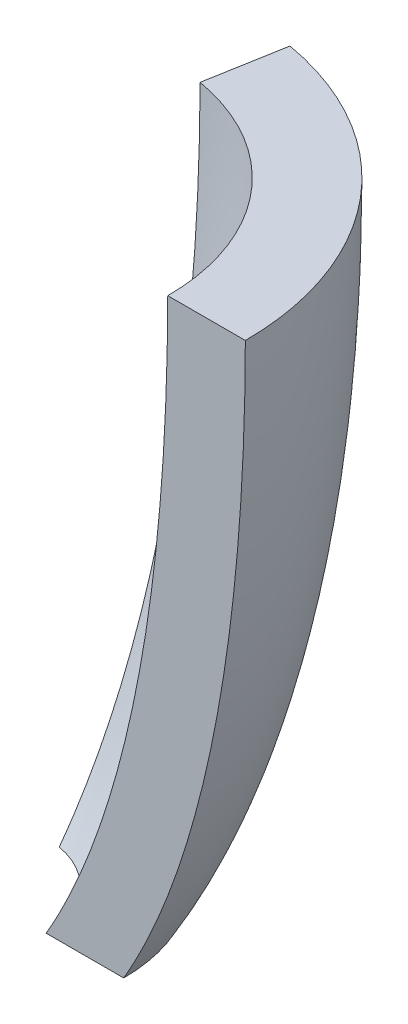
SolidWorks part; units mm, degrees
ref_plane "Front Plane" through (0, 0, 0) normal (0, 0, 1) x (1, 0, 0)
ref_plane "Top Plane" through (0, 0, 0) normal (0, 1, 0) x (1, 0, 0)
ref_plane "Right Plane" through (0, 0, 0) normal (1, 0, 0) x (0, 0, -1)
sketch "Sketch1" plane through (0, 0, 0) normal (0, 0, 1) x (1, 0, 0)
  line L0 (0, 0) -> (35, 0) construction
  line L1 (0, 0) -> (0, -93.4) construction
  line L2 (36.3, 0) -> (26.3, 0)
  line L4 (35, 0) -> (36.3, 0) construction
  line L5 (0, -93.4) -> (0, -94.7)
  line L6 (20.6222, -79.0125) -> (10.6222, -79.0125)
  spline S0 degree 3 poles (26.3, 0) (26.2301, -33.296) (21.1355, -60.9232) (10.6222, -79.0125) knots 0 0 0 0 1 1 1 1
  spline S2 degree 3 poles (36.3, 0) (36.2301, -33.296) (31.1355, -60.9232) (20.6222, -79.0125) knots 0 0 0 0 1 1 1 1
  dimension "D1" = 1.3
  dimension "D2" = 93.4
  dimension "D3" = 35
  dimension "D4" = 1.3
  dimension "D5" = 10
  dimension "D6" = 10
revolve "Revolve1" add sketch "Sketch1" angle 80 about L1
